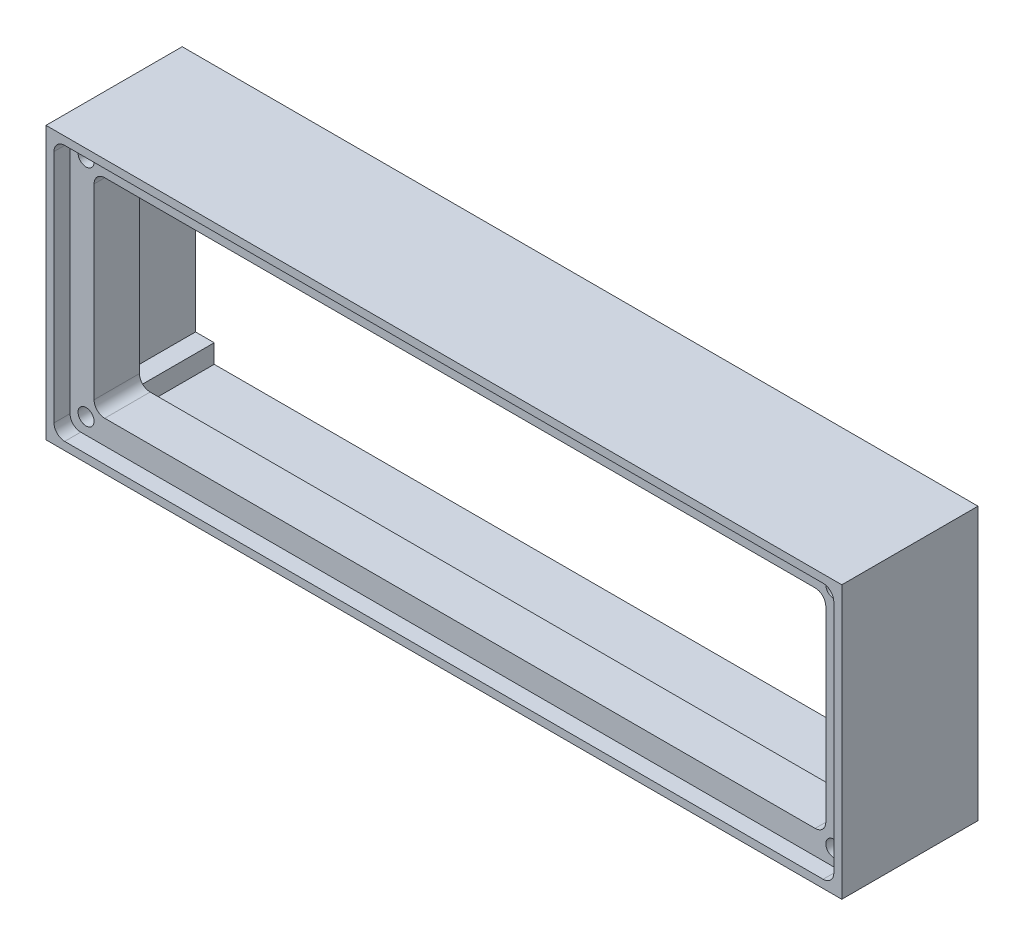
SolidWorks part; units mm, degrees
material "ABS"
ref_plane "Front Plane" through (0, 0, 0) normal (0, 0, 1) x (1, 0, 0)
ref_plane "Top Plane" through (0, 0, 0) normal (0, 1, 0) x (1, 0, 0)
ref_plane "Right Plane" through (0, 0, 0) normal (1, 0, 0) x (0, 0, -1)
sketch "Sketch1" plane through (0, 0, 0) normal (0, 0, 1) x (1, 0, 0)
  line L1 (0, 0) -> (149, 0)
  line L2 (0, 0) -> (0, 51)
  line L3 (0, 51) -> (149, 51)
  line L4 (149, 0) -> (149, 51)
  dimension "D1" = 149
  dimension "D2" = 51
extrude "Extrude-Thin1" add sketch "Sketch1" along normal blind 25.5 thin thin type one direction reverse wall 6
sketch "Sketch2" plane through (0, 0, 25.5) normal (0, 0, 1) x (1, 0, 0)
  line L8 (1.5, 49.5) -> (1.5, 1.5)
  line L9 (1.5, 1.5) -> (147.5, 1.5)
  line L10 (147.5, 1.5) -> (147.5, 49.5)
  line L11 (147.5, 49.5) -> (1.5, 49.5)
  line L12 (1.5, 49.5) -> (1.5, 1.5)
  line L13 (1.5, 1.5) -> (147.5, 1.5)
  line L14 (147.5, 1.5) -> (147.5, 49.5)
  line L15 (147.5, 49.5) -> (1.5, 49.5)
  dimension "D1" = 1.5
extrude "Cut-Extrude1" cut sketch "Sketch2" against normal blind 3 contours L12 L13 L14 L15
sketch "Sketch3" plane through (0, 0, 22.5) normal (0, 0, 1) x (1, 0, 0)
  line L8 (144.5, 46.5) -> (4.5, 46.5)
  line L9 (4.5, 46.5) -> (4.5, 4.5)
  line L10 (4.5, 4.5) -> (144.5, 4.5)
  line L11 (144.5, 4.5) -> (144.5, 46.5)
  line L12 (144.5, 46.5) -> (4.5, 46.5)
  line L13 (4.5, 46.5) -> (4.5, 4.5)
  line L14 (4.5, 4.5) -> (144.5, 4.5)
  line L15 (144.5, 4.5) -> (144.5, 46.5)
  circle A0 centre (4.5, 46.5) radius 1.5
  circle A1 centre (4.5, 4.5) radius 1.5
  circle A3 centre (144.5, 4.5) radius 1.5
  circle A4 centre (144.5, 46.5) radius 1.5
  dimension "D2" = 3
  dimension "D1" = 3
extrude "Cut-Extrude2" cut sketch "Sketch3" against normal blind 8 contours L12 A0 L13 | L13 A0 L12 | L14 A1 L13 | L13 A1 L14 | L15 A4 L12 | L12 A4 L15 | L14 A3 L15 | L15 A3 L14
sketch "Sketch4" plane through (0, 0, 0) normal (0, 0, -1) x (-1, 0, 0)
  line L8 (-3, 3) -> (-3, 48)
  line L9 (-3, 48) -> (-146, 48)
  line L10 (-146, 48) -> (-146, 3)
  line L11 (-146, 3) -> (-3, 3)
  line L12 (-3, 3) -> (-3, 48)
  line L13 (-3, 48) -> (-146, 48)
  line L14 (-146, 48) -> (-146, 3)
  line L15 (-146, 3) -> (-3, 3)
  circle A0 centre (-146, 48) radius 1.5
  circle A1 centre (-3, 48) radius 1.5
  circle A2 centre (-3, 3) radius 1.5
  circle A3 centre (-146, 3) radius 1.5
  dimension "D2" = 3
  dimension "D1" = 3
extrude "Cut-Extrude3" cut sketch "Sketch4" against normal blind 8 contours L13 A0 L14 | L14 A3 L15 | L15 A3 L14 | L14 A0 L13 | L13 A1 L12 | L12 A1 L13 | L15 A2 L12 | L12 A2 L15
sketch "Sketch6" plane through (0, 0, 0) normal (0, 0, -1) x (-1, 0, 0)
  line L0 (-143, 45) -> (-146.5, 45)
  line L1 (-143, 6) -> (-146.5, 6)
  line L2 (-146.5, 6) -> (-146.5, 45)
  line L3 (-74.5, 51) -> (-74.5, 0) construction
  line L4 (-149, 51) -> (0, 51) construction
  line L5 (0, 0) -> (-149, 0) construction
  line L6 (-143, 45) -> (-143, 48.5)
  line L7 (-143, 48.5) -> (-6, 48.5)
  line L8 (-143, 6) -> (-143, 2.5)
  line L9 (-143, 2.5) -> (-6, 2.5)
  line L10 (-6, 6) -> (-6, 2.5)
  line L11 (-6, 6) -> (-2.5, 6)
  line L12 (-2.5, 6) -> (-2.5, 45)
  line L13 (-6, 45) -> (-2.5, 45)
  line L14 (-6, 45) -> (-6, 48.5)
  point P17 (-74.5, 2.5)
  point P22 (-74.5, 48.5)
  dimension "D1" = 3.5
fillet "Fillet1" radius 2 4 edges at (147.5, 1.5, 24) (147.5, 49.5, 24) (1.5, 49.5, 24) (1.5, 1.5, 24)
fillet "Fillet2" radius 2 4 edges at (143, 45, 11.25) (143, 6, 11.25) (6, 6, 11.25) (6, 45, 11.25)
extrude "Cut-Extrude7" cut sketch "Sketch6" against normal blind 14 contours L9 L10 L11 L12 L13 L14 L7 L6 L0 L2 L1 L8
